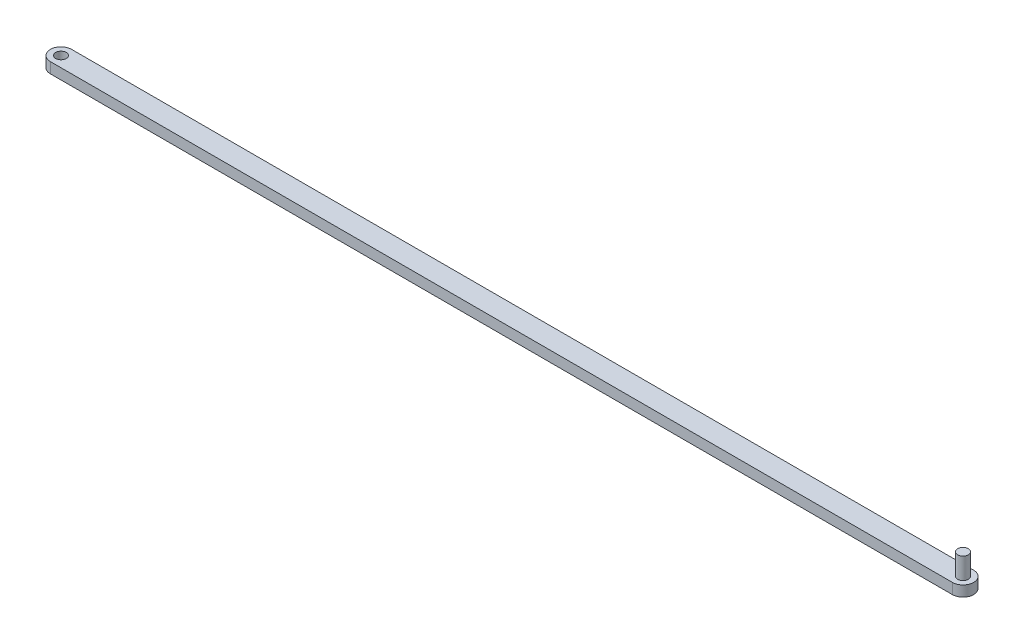
SolidWorks part; units mm, degrees
ref_plane "Front Plane" through (0, 0, 0) normal (0, 0, 1) x (1, 0, 0)
ref_plane "Top Plane" through (0, 0, 0) normal (0, 1, 0) x (1, 0, 0)
ref_plane "Right Plane" through (0, 0, 0) normal (1, 0, 0) x (0, 0, -1)
sketch "Sketch5" plane through (0, 0, 0) normal (0, 1, 0) x (1, 0, 0)
  line L0 (-425, 0) -> (425, 0) construction
  line L1 (-425, 10) -> (425, 10)
  line L2 (-425, -10) -> (425, -10)
  arc A0 (-425, 10) -> (-425, -10) centre (-425, 0) ccw
  arc A1 (425, -10) -> (425, 10) centre (425, 0) ccw
  circle A2 centre (-425, 0) radius 5
  point P2 (0, 0)
  dimension "D2" = 10
  dimension "D3" = 10
  dimension "D1" = 850
extrude "Boss-Extrude1" add sketch "Sketch5" against normal blind 10
sketch "Sketch7" plane through (0, 0, 0) normal (0, 1, 0) x (1, 0, 0)
  circle A0 centre (425, 0) radius 5
  dimension "D1" = 10
extrude "Boss-Extrude2" add sketch "Sketch7" along normal blind 20
